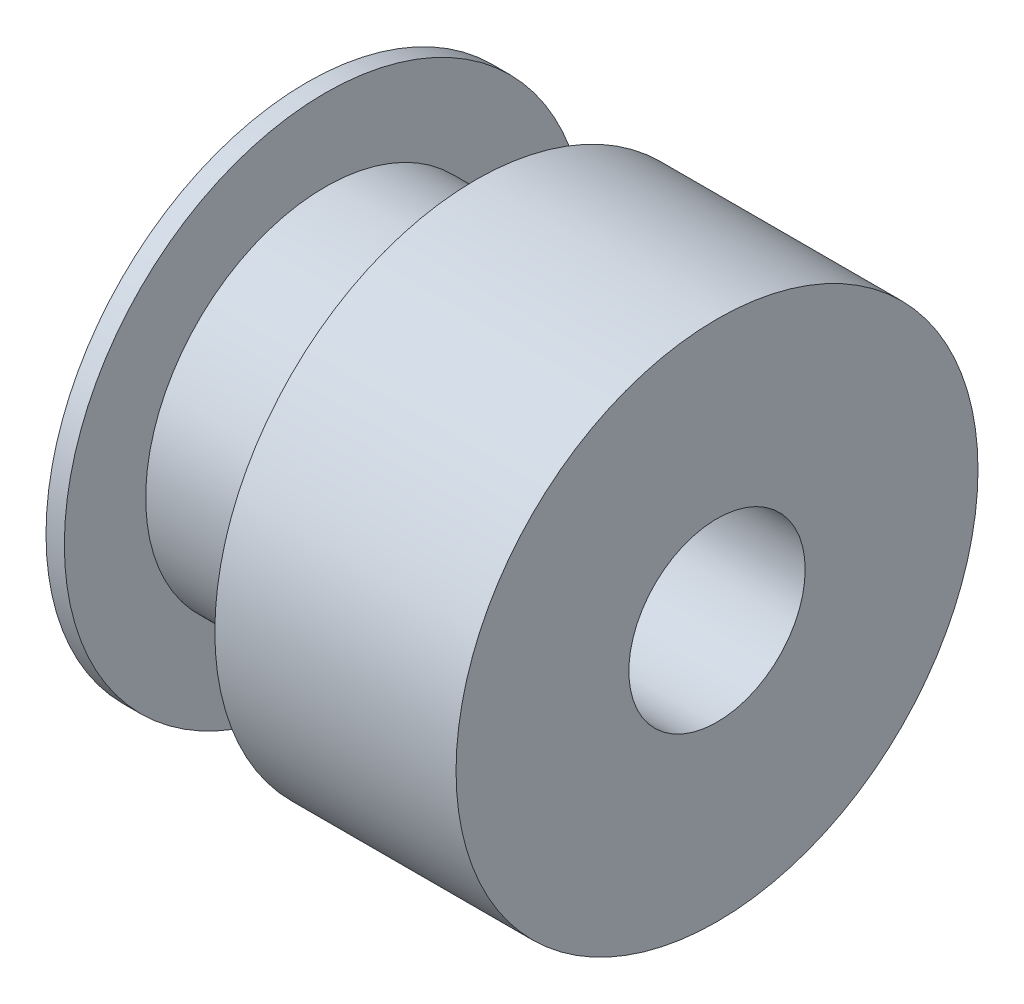
SolidWorks part; units mm, degrees
ref_plane "Front Plane" through (0, 0, 0) normal (0, 0, 1) x (1, 0, 0)
ref_plane "Top Plane" through (0, 0, 0) normal (0, 1, 0) x (1, 0, 0)
ref_plane "Right Plane" through (0, 0, 0) normal (1, 0, 0) x (0, 0, -1)
sketch "Sketch1" plane through (0, 0, 0) normal (1, 0, 0) x (0, 0, -1)
  circle A0 centre (0, 0) radius 7.0485
  dimension "D1" = 14.097
extrude "Boss-Extrude1" add sketch "Sketch1" along normal blind 0.4953
sketch "Sketch2" plane through (0.4953, 0, 0) normal (1, 0, 0) x (0, 0, -1)
  circle A0 centre (0, 0) radius 4.8514
  dimension "D1" = 9.7028
extrude "Boss-Extrude2" add sketch "Sketch2" along normal blind 4.064
sketch "Sketch3" plane through (4.5593, 0, 0) normal (1, 0, 0) x (0, 0, -1)
  circle A0 centre (0, 0) radius 7.0485
  circle A1 centre (0, 0) radius 7.0485 construction
extrude "Boss-Extrude3" add sketch "Sketch3" along normal blind 0.4953
sketch "Sketch4" plane through (5.0546, 0, 0) normal (1, 0, 0) x (0, 0, -1)
  circle A0 centre (0, 0) radius 7.0485
extrude "Boss-Extrude4" add sketch "Sketch4" along normal blind 6.0198
sketch "Sketch5" plane through (11.0744, 0, 0) normal (1, 0, 0) x (0, 0, -1)
  circle A0 centre (0, 0) radius 2.3813
  dimension "D1" = 4.7625
extrude "Cut-Extrude1" cut sketch "Sketch5" against normal through all
